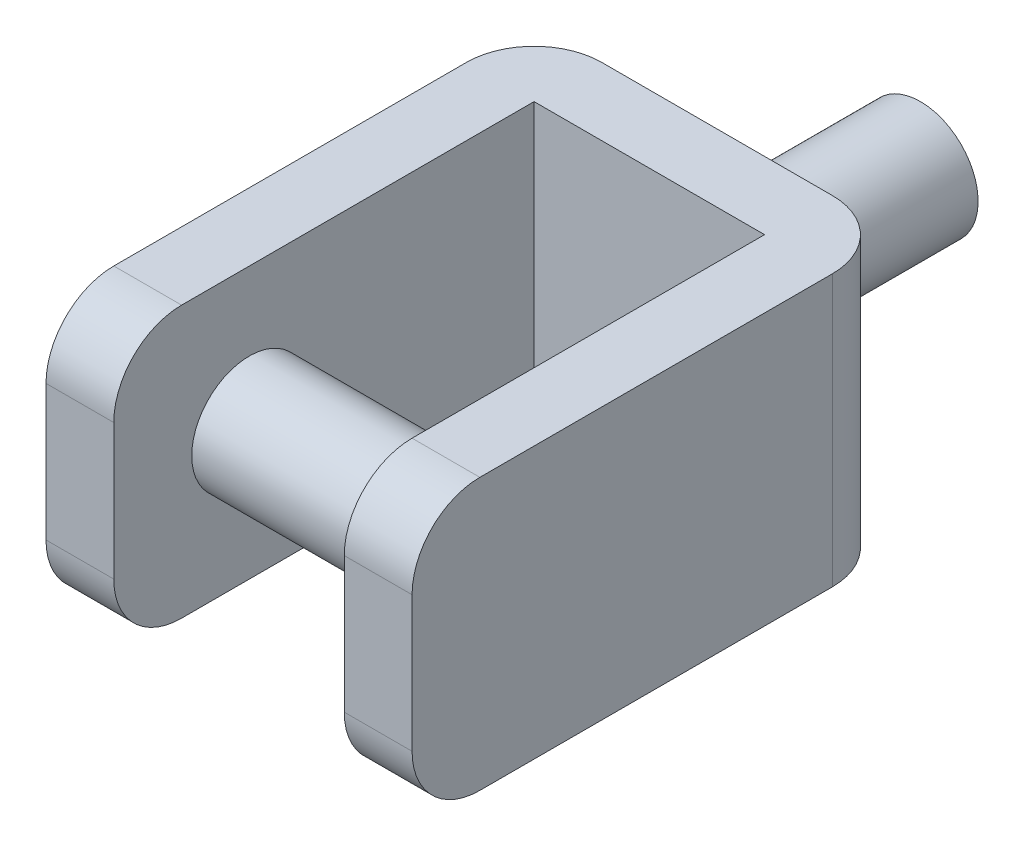
SolidWorks part; units mm, degrees
ref_plane "Front Plane" through (0, 0, 0) normal (0, 0, 1) x (1, 0, 0)
ref_plane "Top Plane" through (0, 0, 0) normal (0, 1, 0) x (1, 0, 0)
ref_plane "Right Plane" through (0, 0, 0) normal (1, 0, 0) x (0, 0, -1)
sketch "Sketch1" plane through (0, 0, 0) normal (0, 1, 0) x (1, 0, 0)
  line L0 (-37.1337, -33.4467) -> (-62.5337, -33.4467)
  line L1 (-37.1337, 124.0333) -> (49.2263, 124.0333)
  line L2 (-37.1337, 124.0333) -> (-37.1337, -33.4467)
  line L4 (49.2263, 124.0333) -> (49.2263, -33.4467)
  line L5 (-62.5337, -33.4467) -> (-62.5337, 149.4333)
  line L6 (-62.5337, 149.4333) -> (74.6263, 149.4333)
  line L7 (74.6263, 149.4333) -> (74.6263, -33.4467)
  line L8 (74.6263, -33.4467) -> (49.2263, -33.4467)
  dimension "D1" = 86.36
  dimension "D2" = 157.48
  dimension "D3" = 25.4
  dimension "D4" = 25.4
  dimension "D5" = 137.16
  dimension "D6" = 25.4
  dimension "D7" = 157.48
extrude "Boss-Extrude1" add sketch "Sketch1" along normal blind 101.6
sketch "Sketch3" plane through (-37.1337, 0, 0) normal (1, 0, 0) x (0, 0, -1)
  line L0 (17.3533, 101.6) -> (17.3533, 0) construction
  line L1 (-33.4467, 101.6) -> (124.0333, 101.6) construction
  line L2 (-33.4467, 0) -> (124.0333, 0) construction
  line L5 (124.0333, 101.6) -> (124.0333, 0) construction
  circle A0 centre (17.3533, 50.8) radius 21.59
  dimension "D2" = 43.18
  dimension "D1" = 106.68
extrude "Boss-Extrude2" add sketch "Sketch3" along normal up to next
sketch "Sketch4" plane through (0, 0, -149.4333) normal (0, 0, -1) x (-1, 0, 0)
  line L0 (-74.6263, 101.6) -> (62.5337, 0) construction
  circle A0 centre (-6.0463, 50.8) radius 21.59
  dimension "D1" = 43.18
extrude "Boss-Extrude3" add sketch "Sketch4" along normal blind 76.2
fillet "Fillet1" radius 25.4 2 edges at (-49.8337, 101.6, 33.4467) (-49.8337, 0, 33.4467)
fillet "Fillet2" radius 25.4 1 edges at (-62.5337, 50.8, -149.4333)
fillet "Fillet4" radius 25.4 2 edges at (61.9263, 0, 33.4467) (61.9263, 101.6, 33.4467)
fillet "Fillet5" radius 25.4 1 edges at (74.6263, 50.8, -149.4333)
